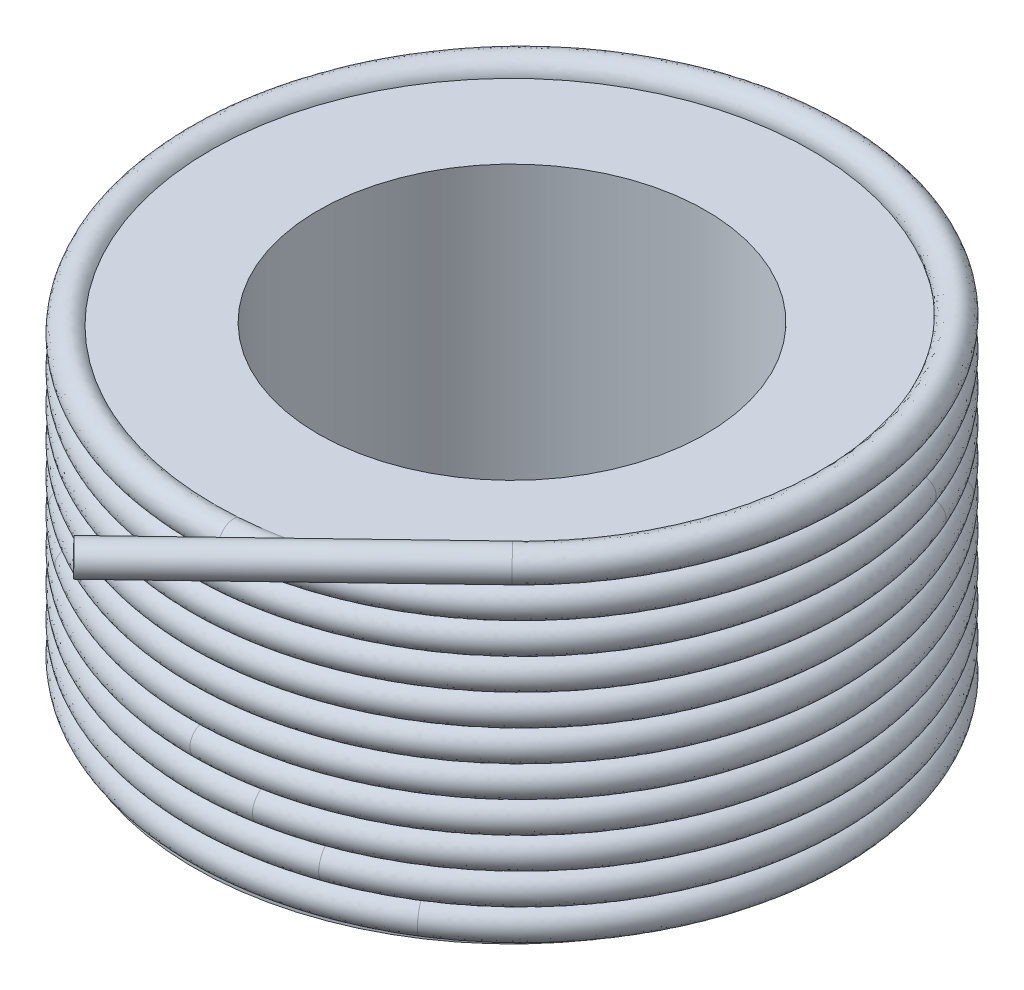
SolidWorks part; units mm, degrees
ref_plane "Front Plane" through (0, 0, 0) normal (0, 0, 1) x (1, 0, 0)
ref_plane "Top Plane" through (0, 0, 0) normal (0, 1, 0) x (1, 0, 0)
ref_plane "Right Plane" through (0, 0, 0) normal (1, 0, 0) x (0, 0, -1)
sketch "Sketch1" plane through (0, 0, 0) normal (0, 1, 0) x (1, 0, 0)
  circle A0 centre (0, 0) radius 10
  circle A1 centre (0, 0) radius 16.4
extrude "Boss-Extrude1" add sketch "Sketch1" along normal blind 16.1 and the other way blind 0.1
sketch "Sketch2" plane through (0, 0, 0) normal (0, 1, 0) x (1, 0, 0)
  circle A0 centre (0, 0) radius 16.21
curve "Helix/Spiral1" pitch 1.6 height 16.8 turns 10.5
sweep "Sweep3" add path "Helix/Spiral1" circular profile diameter 1.6 parameters "D3"=1.6
sketch "Sketch18" plane through (-0.1866, 0.0041, 0.1866) normal (-0.707, 0.0157, 0.707) x (0.7068, -0.0157, 0.7072)
  circle A0 centre (15.9442, 17.0504) radius 0.8
extrude "Boss-Extrude3" add sketch "Sketch18" along normal blind 16 separate body
sketch "Sketch20" plane through (0, 0, 0) normal (-0.707, -0.0157, 0.707) x (0.7068, 0.0157, 0.7072)
  circle A1 centre (-16.208, 0.2546) radius 0.8
extrude "Boss-Extrude4" add sketch "Sketch20" along normal blind 16 separate body
